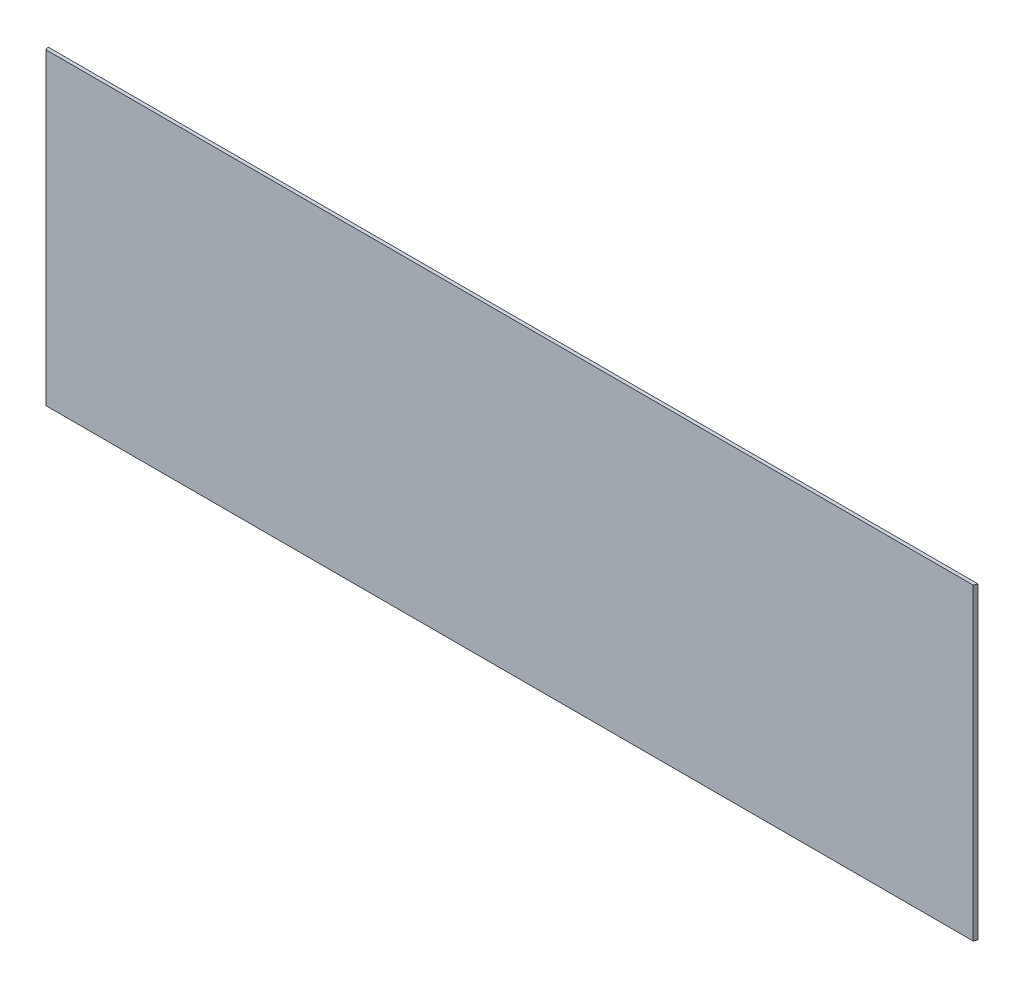
SolidWorks part; units mm, degrees
material "6061 Alloy"
ref_plane "Front Plane" through (0, 0, 0) normal (0, 0, 1) x (1, 0, 0)
ref_plane "Top Plane" through (0, 0, 0) normal (0, 1, 0) x (1, 0, 0)
ref_plane "Right Plane" through (0, 0, 0) normal (1, 0, 0) x (0, 0, -1)
sketch "Sketch1" plane through (0, 0, 0) normal (0, 1, 0) x (1, 0, 0)
  line L0 (431.038, 1.5875) -> (429.7229, -1.5875)
  line L1 (-431.038, 1.5875) -> (431.038, 1.5875)
  line L3 (-429.7229, -1.5875) -> (429.7229, -1.5875)
  line L5 (-431.038, 1.5875) -> (429.7249, -1.5827) construction
  line L6 (-429.7249, -1.5827) -> (431.038, 1.5875) construction
  line L7 (-431.038, 1.5875) -> (-429.7229, -1.5875)
  point P0 (0, 0)
  dimension "D1" = 862.076
  dimension "D2" = 67.5
  dimension "D3" = 67.5
  dimension "D4" = 431.038
extrude "Extrude1" add sketch "Sketch1" along normal mid plane 285.75
